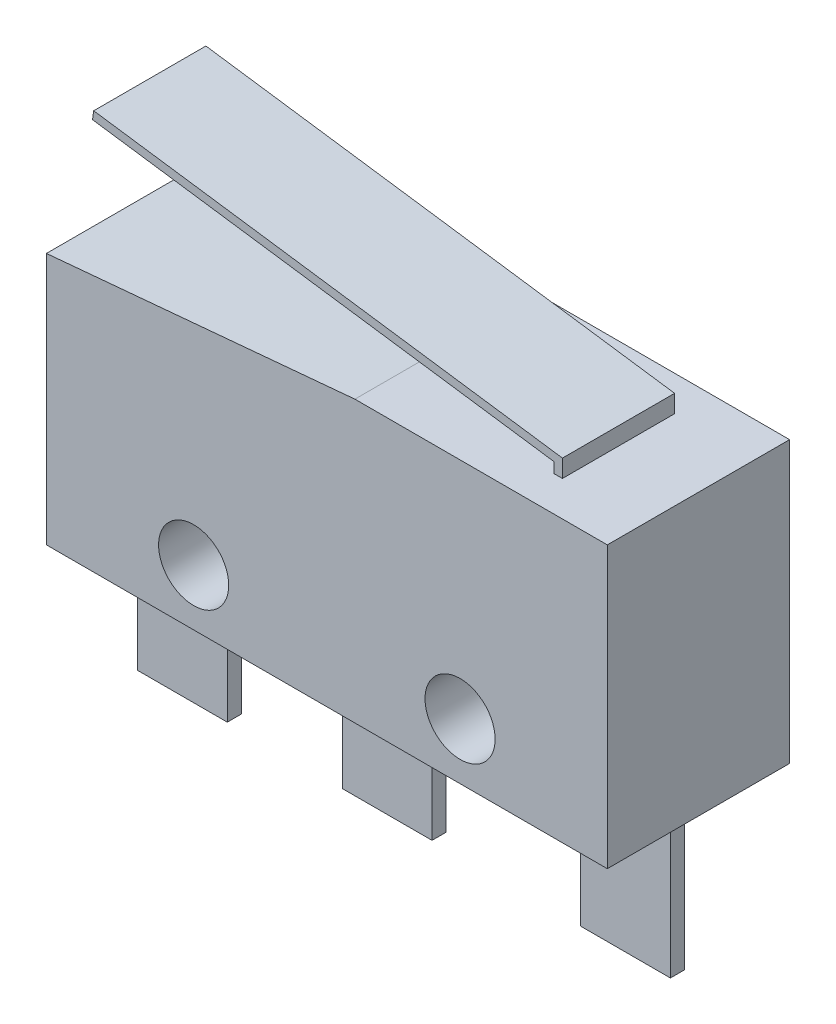
SolidWorks part; units mm, degrees
ref_plane "Front" through (0, 0, 0) normal (0, 0, 1) x (1, 0, 0)
ref_plane "Top" through (0, 0, 0) normal (0, 1, 0) x (1, 0, 0)
ref_plane "Right" through (0, 0, 0) normal (1, 0, 0) x (0, 0, -1)
sketch "Sketch1" plane through (0, 0, 0) normal (0, 0, 1) x (1, 0, 0)
  line L1 (-10, 10) -> (10, 10)
  line L2 (-10, 10) -> (-10, 0)
  line L3 (-10, 0) -> (10, 0)
  line L4 (10, 10) -> (10, 0)
  dimension "D1" = 20
  dimension "D2" = 10
extrude "Boss-Body" add sketch "Sketch1" along normal mid plane 6.5
sketch "Sketch2" plane through (0, 0, 3.25) normal (0, 0, 1) x (1, 0, 0)
  line L0 (1, 10) -> (-10, 9)
  line L1 (10, 10) -> (-10, 10) construction
  line L2 (-10, 10) -> (-10, 0) construction
  line L3 (-10, 9) -> (-10, 10)
  line L4 (-10, 10) -> (1, 10)
  line L5 (10, 0) -> (10, 10) construction
  dimension "D1" = 9
  dimension "D2" = 1
extrude "Cut-Top Angle" cut sketch "Sketch2" against normal through all
sketch "Sketch3" plane through (0, 0, 0) normal (0, 0, 1) x (1, 0, 0)
  line L0 (10, 10) -> (1, 10) construction
  line L1 (2, 10) -> (4, 10)
  line L2 (2, 10) -> (2, 10.5)
  line L3 (2, 10.5) -> (4, 10.5)
  line L4 (4, 10) -> (4, 10.5)
  line L5 (10, 0) -> (10, 10) construction
  dimension "D1" = 6
  dimension "D2" = 2
  dimension "D3" = 0.5
extrude "Boss-Button" add sketch "Sketch3" along normal mid plane 2
sketch "Sketch4" plane through (0, 0, 0) normal (0, 0, 1) x (1, 0, 0)
  line L0 (1.0527, 11.1) -> (4.7219, 11.1) construction
  line L1 (4, 10.5) -> (2, 10.5) construction
  line L2 (2, 10.5) -> (4, 10.5)
  arc A0 (2, 10.5) -> (4, 10.5) centre (3, 9.9667) cw
  dimension "D1" = 0.6
extrude "Boss-Button Round Top" add sketch "Sketch4" along normal mid plane 2
sketch "Sketch5" plane through (0, 0, 3.25) normal (0, 0, 1) x (1, 0, 0)
  line L0 (0, 0) -> (0, 9.9091) construction
  line L1 (-10, 9) -> (1, 10) construction
  line L2 (-4.75, 2) -> (4.75, 2) construction
  line L3 (-10, 0) -> (10, 0) construction
  circle A0 centre (-4.75, 2) radius 1.25
  circle A1 centre (4.75, 2) radius 1.25
  point P9 (0, 2)
  dimension "D2" = 2.5
  dimension "D1" = 9.5
  dimension "D3" = 2
extrude "Cut-Extrude2" cut sketch "Sketch5" against normal through all
sketch "Sketch6" plane through (0, 0, 0) normal (0, 0, 1) x (1, 0, 0)
  line L0 (-10, 0) -> (10, 0) construction
  line L1 (-9.5, 0) -> (-6.3, 0)
  line L2 (-9.5, 0) -> (-9.5, -5)
  line L3 (-9.5, -5) -> (-6.3, -5)
  line L4 (-6.3, 0) -> (-6.3, -5)
  line L5 (-10, 9) -> (-10, 0) construction
  line L6 (0, 0) -> (0, 9.9091) construction
  line L7 (-10, 9) -> (1, 10) construction
  line L8 (6.3, 0) -> (6.3, -5)
  line L9 (9.5, -5) -> (6.3, -5)
  line L10 (9.5, 0) -> (9.5, -5)
  line L11 (9.5, 0) -> (6.3, 0)
  line L12 (10, 0) -> (10, 10) construction
  line L13 (-2.2, 0) -> (1, 0)
  line L14 (-2.2, 0) -> (-2.2, -5)
  line L15 (-2.2, -5) -> (1, -5)
  line L16 (1, 0) -> (1, -5)
  dimension "D1" = 5
  dimension "D2" = 3.2
  dimension "D3" = 0.5
  dimension "D4" = 9
extrude "Boss-Extrude4" add sketch "Sketch6" along normal blind 0.5
sketch "Sketch7" plane through (0, 0, 0) normal (0, 0, 1) x (1, 0, 0)
  line L0 (7, 10) -> (7, 10.5)
  line L1 (10, 10) -> (1, 10) construction
  line L2 (7, 10.5) -> (-9.5843, 12.85)
  line L3 (10, 0) -> (10, 10) construction
  dimension "D1" = 16.75
  dimension "D2" = 3
  dimension "D3" = 0.5
  dimension "D4" = 3.85
extrude "Extrude-Thin1" add sketch "Sketch7" along normal mid plane 4 thin thin type mid plane wall 0.3
